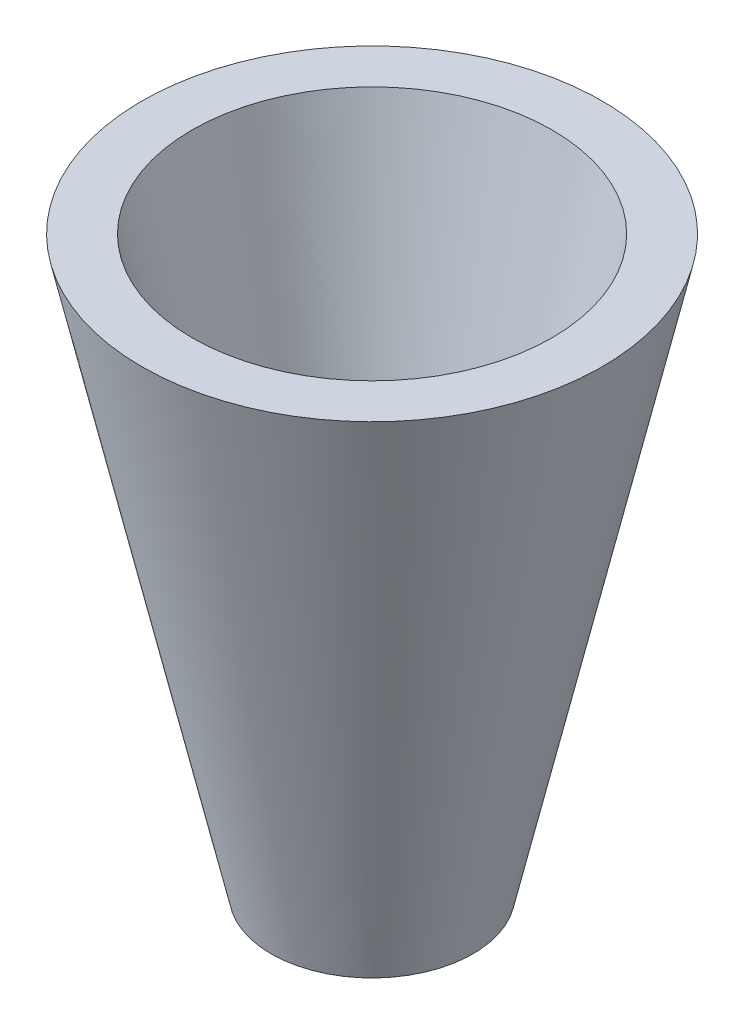
SolidWorks part; units mm, degrees
ref_plane "Alzado" through (0, 0, 0) normal (0, 0, 1) x (1, 0, 0)
ref_plane "Planta" through (0, 0, 0) normal (0, 1, 0) x (1, 0, 0)
ref_plane "Vista lateral" through (0, 0, 0) normal (1, 0, 0) x (0, 0, -1)
sketch "Croquis1" plane through (0, 0, 0) normal (0, 0, 1) x (1, 0, 0)
  line L0 (0, 55.4679) -> (0, -61.711)
  line L1 (0, -61.711) -> (20.6504, -61.711)
  line L2 (20.6504, -61.711) -> (47.0637, 55.4679)
  line L3 (47.0637, 55.4679) -> (0, 55.4679)
revolve "Revolución1" add sketch "Croquis1" angle 360 about L0
shell "Vaciado1" thickness 10
